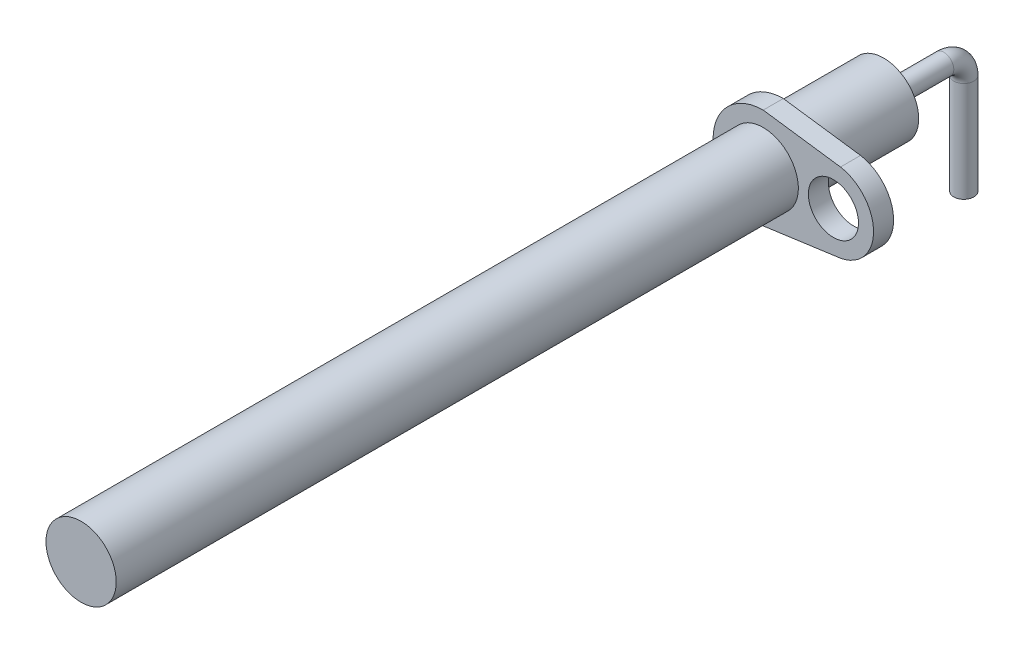
SolidWorks part; units mm, degrees
ref_plane "Front Plane" through (0, 0, 0) normal (0, 0, 1) x (1, 0, 0)
ref_plane "Top Plane" through (0, 0, 0) normal (0, 1, 0) x (1, 0, 0)
ref_plane "Right Plane" through (0, 0, 0) normal (1, 0, 0) x (0, 0, -1)
sketch "Sketch1" plane through (0, 0, 0) normal (0, 0, 1) x (1, 0, 0)
  circle A0 centre (0, 0) radius 1.75
  dimension "D1" = 3.5
extrude "Boss-Extrude1" add sketch "Sketch1" along normal blind 40
sketch3d "3DSketch1"
  line L0 (0, 0, 0) -> (0, 0, -3)
  line L1 (0, -1, -4) -> (0, -6, -4)
  arc A0 (0, 0, -3) -> (0, -1, -4) centre (0, -1, -3) ccw
  point P6 (0, 0, -4)
  point P7 (-1, -1, -3)
  point P8 (-4.0958, 0, -4.0812)
  dimension "D3" = 1
  dimension "D1" = 4
  dimension "D2" = 6
sweep "Sweep1" add path "3DSketch1" circular profile diameter 1 parameters "D3"=1
ref_plane "Plane1" through (0, 0, 6) normal (0, 0, -1) x (-1, 0, 0)
sketch "Sketch16" plane through (0, 0, 6) normal (0, 0, -1) x (-1, 0, 0)
  line L0 (0, 2.5) -> (0, -2.5) construction
  line L1 (-5.5, 0) -> (2.5, 0) construction
  line L2 (-3.8516, 1.9689) -> (0, 2.5)
  line L3 (-3.8516, -1.9689) -> (0, -2.5)
  arc A0 (0, 2.5) -> (0, -2.5) centre (0, 0) cw
  circle A1 centre (0, 0) radius 1.75 construction
  arc A2 (-3.8516, 1.9689) -> (-3.8516, -1.9689) centre (-3.5, 0) ccw
  circle A3 centre (-3.5, 0) radius 1.25
  dimension "D1" = 2.5
  dimension "D3" = 2
  dimension "D4" = 2.5
  dimension "D2" = 8
extrude "Boss-Extrude2" add sketch "Sketch16" along normal blind 1 contours L2 A2 L3 A0 A3
